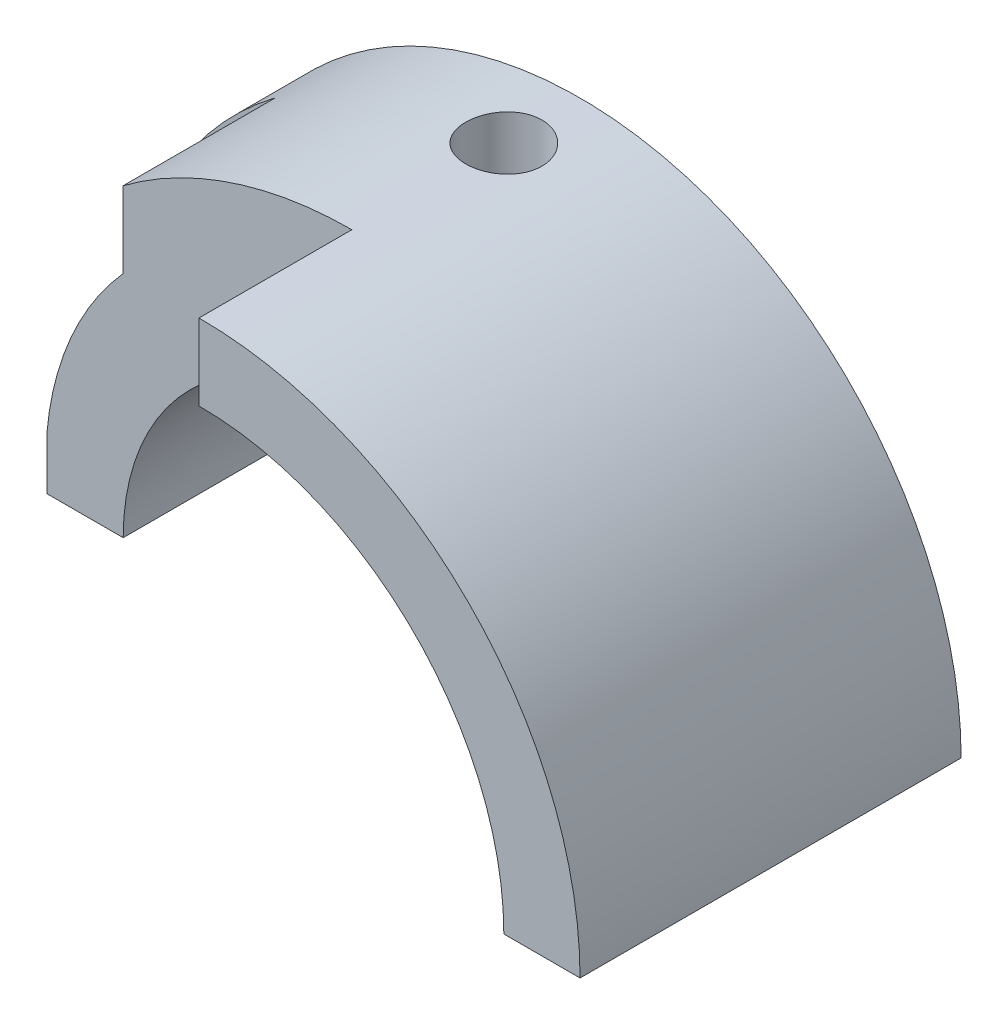
SolidWorks part; units mm, degrees
ref_plane "Front Plane" through (0, 0, 0) normal (0, 0, 1) x (1, 0, 0)
ref_plane "Top Plane" through (0, 0, 0) normal (0, 1, 0) x (1, 0, 0)
ref_plane "Right Plane" through (0, 0, 0) normal (1, 0, 0) x (0, 0, -1)
sketch "Sketch1" plane through (0, 0, 0) normal (0, 0, 1) x (1, 0, 0)
  line L0 (-5, 0) -> (-3, 0)
  line L1 (3, 0) -> (5, 0)
  arc A0 (5, 0) -> (-5, 0) centre (0, 0) ccw
  arc A1 (3, 0) -> (-3, 0) centre (0, 0) ccw
extrude "Boss-Extrude1" add sketch "Sketch1" along normal blind 5
sketch "Sketch2" plane through (0, 0, 0) normal (0, 1, 0) x (1, 0, 0)
  line L0 (-5, -1) -> (-4.0013, -1)
  line L1 (-5, -5) -> (-5, 0) construction
  line L2 (-4.0013, -1) -> (-4.0013, -1.9975)
  line L3 (-4.0013, -1.9975) -> (-4.0013, -2.9945)
  line L4 (-4.0013, -2.9945) -> (0, -2.9945)
  line L5 (0, -2.9945) -> (0, -5)
  line L6 (-5, -5) -> (5, -5) construction
  line L7 (0, -5) -> (-5, -5)
  line L8 (-5, -5) -> (-5, -1)
  circle A0 centre (0, -1) radius 0.5
  dimension "D1" = 1
  dimension "D2" = 1
extrude "Cut-Extrude1" cut sketch "Sketch2" along normal blind 5
sketch "Sketch3" plane through (0, 0, 5) normal (0, 0, 1) x (1, 0, 0)
  line L0 (0, 5) -> (0, 3) construction
  line L1 (3, 0) -> (5, 0) construction
  line L2 (0, 4) -> (0, 0)
  line L3 (0, 0) -> (4, 0)
  arc A0 (0, 4) -> (4, 0) centre (0, 0) cw
extrude "Cut-Extrude2" cut sketch "Sketch3" against normal blind 1
sketch "Sketch4" plane through (0, 0, 2.9945) normal (0, 0, 1) x (1, 0, 0)
  line L0 (-3.0013, 3) -> (-3.0013, 3.9991)
  line L1 (-5, 0) -> (-4.0013, 0)
  arc A0 (-4.0013, 0) -> (-3.0013, 3) centre (-0.026, 0.3416) cw
  arc A1 (0, 5) -> (-4.0013, 2.9983) centre (0, 0) ccw construction
  arc A2 (-3.0013, 3.9991) -> (-5, 0) centre (0, 0) ccw
  arc A3 (-4.0013, 2.9983) -> (-5, 0) centre (0, 0) ccw construction
  dimension "D1" = 3
  dimension "D2" = 1
extrude "Cut-Extrude3" cut sketch "Sketch4" against normal blind 2
